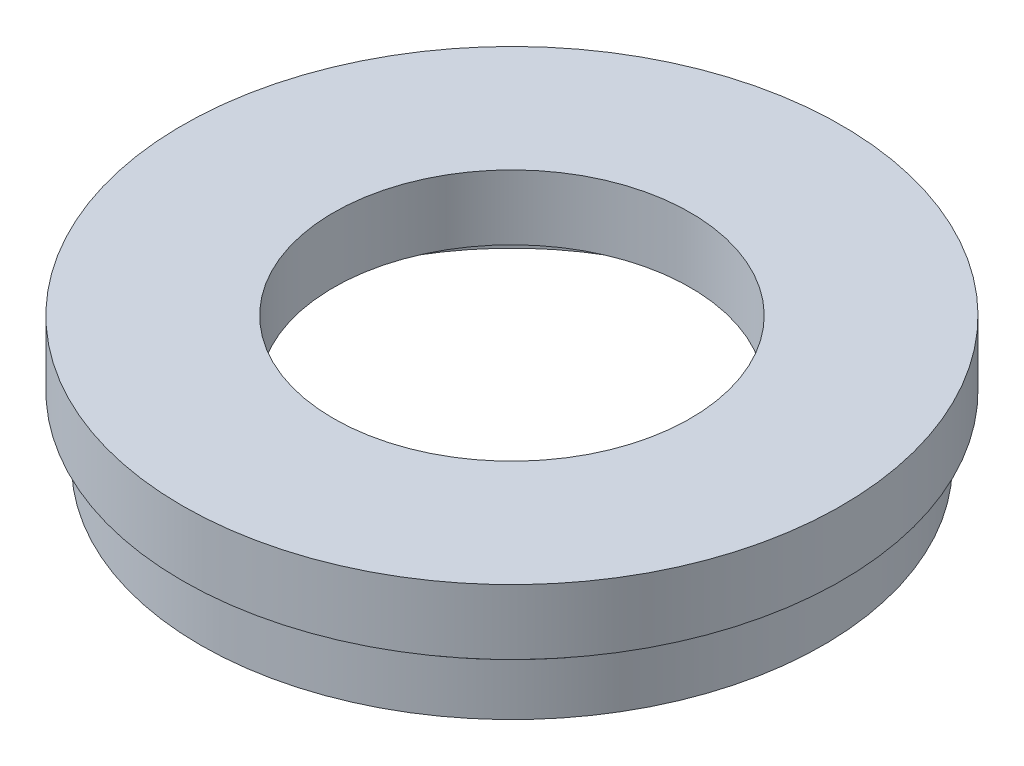
SolidWorks part; units mm, degrees
ref_plane "前视基准面" through (0, 0, 0) normal (0, 0, 1) x (1, 0, 0)
ref_plane "上视基准面" through (0, 0, 0) normal (0, 1, 0) x (1, 0, 0)
ref_plane "右视基准面" through (0, 0, 0) normal (1, 0, 0) x (0, 0, -1)
sketch "草图1" plane through (0, 0, 0) normal (0, 0, 1) x (1, 0, 0)
  line L0 (0, 17.4193) -> (0, -25.7883) construction
  line L1 (20.5, 0) -> (20.5, 4)
  line L2 (20.5, 4) -> (21.1, 4)
  line L3 (21.1, 4) -> (21.1, 5)
  line L4 (21.1, 5) -> (13.75, 5)
  line L5 (13.75, 5) -> (13.75, 10)
  line L6 (13.75, 10) -> (25.4, 10)
  line L7 (20.5, 0) -> (24, 0)
  line L8 (24, 0) -> (24, 4)
  line L9 (24, 4) -> (23.5, 4)
  line L10 (23.5, 4) -> (23.5, 5)
  line L11 (23.5, 5) -> (25.4, 5)
  line L12 (25.4, 5) -> (25.4, 10)
  dimension "D1" = 20.5
  dimension "D2" = 21.1
  dimension "D3" = 13.75
  dimension "D4" = 24
  dimension "D5" = 23.5
  dimension "D6" = 25.4
  dimension "D7" = 1
  dimension "D8" = 1
  dimension "D9" = 5
  dimension "D10" = 10
revolve "旋转1" add sketch "草图1" angle 360 about L0
cosmetic thread "装饰螺纹线1" parameters "D2"=28.5
cosmetic thread "装饰螺纹线2" parameters "D2"=42
cosmetic thread "装饰螺纹线3" parameters "D2"=47
